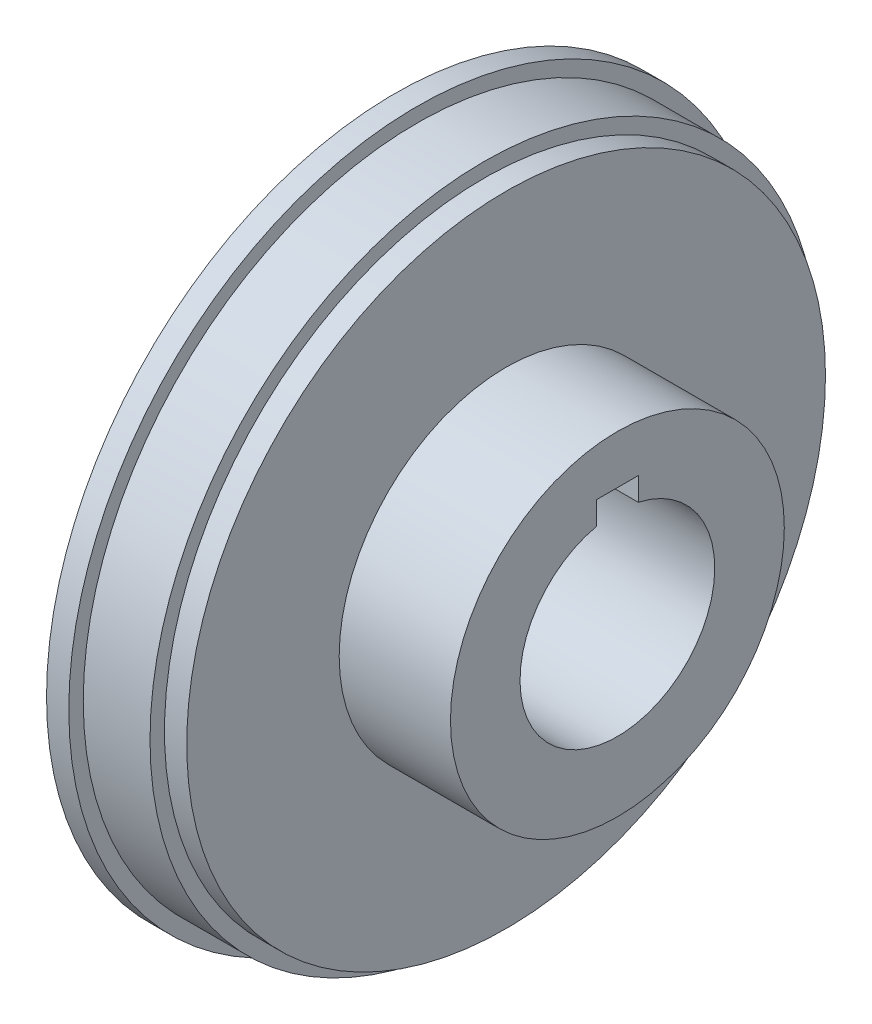
SolidWorks part; units mm, degrees
material "Plain Carbon Steel"
ref_plane "Front Plane" through (0, 0, 0) normal (0, 0, 1) x (1, 0, 0)
ref_plane "Top Plane" through (0, 0, 0) normal (0, 1, 0) x (1, 0, 0)
ref_plane "Right Plane" through (0, 0, 0) normal (1, 0, 0) x (0, 0, -1)
sketch "Sketch1" plane through (0, 0, 0) normal (1, 0, 0) x (0, 0, -1)
  line L0 (0, 13.4937) -> (0, 8.7312) construction
  line L1 (-2.3813, 13.4937) -> (2.3812, 13.4937)
  line L2 (-2.3813, 13.4937) -> (-2.3813, 8.7312)
  line L3 (-2.3813, 8.7312) -> (2.3813, 8.7312)
  line L4 (2.3812, 13.4937) -> (2.3813, 8.7312)
  line L5 (0, 8.7312) -> (2.3812, 11.1125) construction
  line L6 (2.3812, 11.1125) -> (-2.3813, 11.1125) construction
  line L7 (0, 8.7312) -> (0, 0) construction
  circle A0 centre (0, 0) radius 11.1125
  circle A1 centre (0, 0) radius 25.4
  dimension "D1" = 11.1125
  dimension "D4" = 22.225
  dimension "D2" = 2.3813
  dimension "D3" = 4.7625
extrude "Boss-Extrude1" add sketch "Sketch1" along normal blind 25.4 contours A1 A0 L2 L1 L4
sketch "Sketch2" plane through (0, 0, 0) normal (-1, 0, 0) x (0, 0, 1)
  circle A0 centre (0, 0) radius 19.05
  circle A1 centre (0, 0) radius 38.1
extrude "Boss-Extrude2" add sketch "Sketch2" against normal blind 12.7
sketch "Sketch3" plane through (25.4, 0, 0) normal (1, 0, 0) x (0, 0, -1)
  circle A0 centre (0, 0) radius 19.05
  circle A1 centre (0, 0) radius 25.4
extrude "Cut-Extrude1" cut sketch "Sketch3" against normal up to surface (12.7 mm away) up to face at (12.7, 0, 38.1)
sketch "Sketch4" plane through (12.7, 0, 0) normal (1, 0, 0) x (0, 0, -1)
  line L0 (0, 19.05) -> (0, 35.56) construction
  circle A0 centre (0, 0) radius 19.05 construction
  circle A1 centre (0, 0) radius 19.05 construction
  circle A2 centre (0, 27.305) radius 8.89
extrude "Cut-Extrude2" [suppressed] cut sketch "Sketch4" against normal through all
pattern_circular "CirPattern1" [suppressed] count 6 over 360
sketch "Sketch5" plane through (0, 0, 0) normal (-1, 0, 0) x (0, 0, 1)
  circle A0 centre (0, 0) radius 39.751
  circle A1 centre (0, 0) radius 38.1
extrude "Boss-Extrude3" add sketch "Sketch5" against normal blind 2.54
sketch "Sketch6" plane through (12.7, 0, 0) normal (1, 0, 0) x (0, 0, -1)
  circle A0 centre (0, 0) radius 36.449
  circle A1 centre (0, 0) radius 38.1
extrude "Cut-Extrude3" cut sketch "Sketch6" against normal blind 2.54
